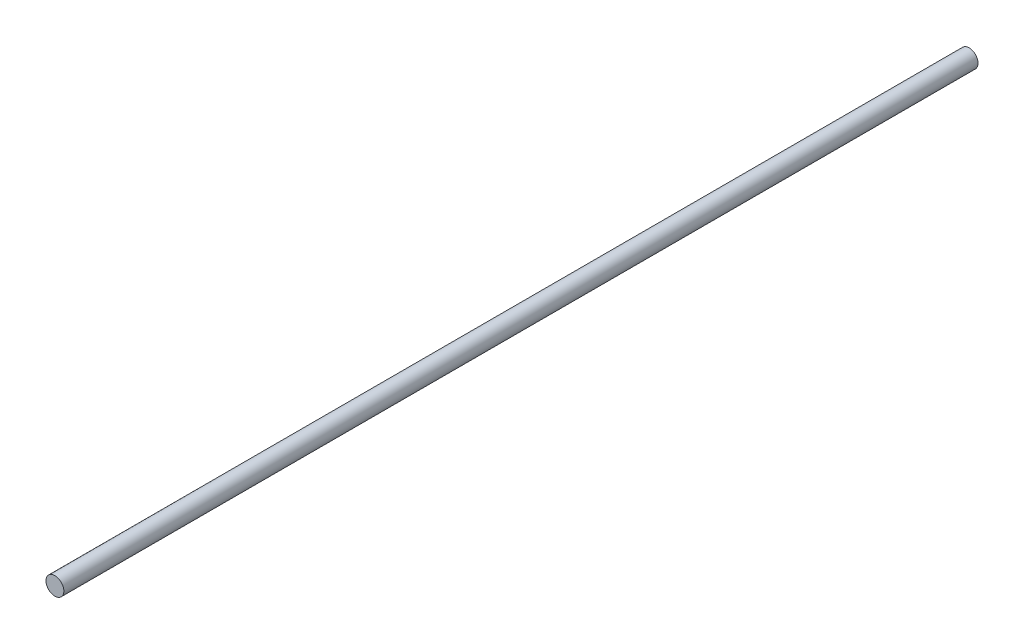
SolidWorks part; units mm, degrees
ref_plane "Front Plane" through (0, 0, 0) normal (0, 0, 1) x (1, 0, 0)
ref_plane "Top Plane" through (0, 0, 0) normal (0, 1, 0) x (1, 0, 0)
ref_plane "Right Plane" through (0, 0, 0) normal (1, 0, 0) x (0, 0, -1)
sketch "Sketch1" plane through (0, 0, 0) normal (0, 0, 1) x (1, 0, 0)
  circle A0 centre (0, 0) radius 4
  dimension "D1" = 8
extrude "Boss-Extrude1" add sketch "Sketch1" along normal mid plane 410
